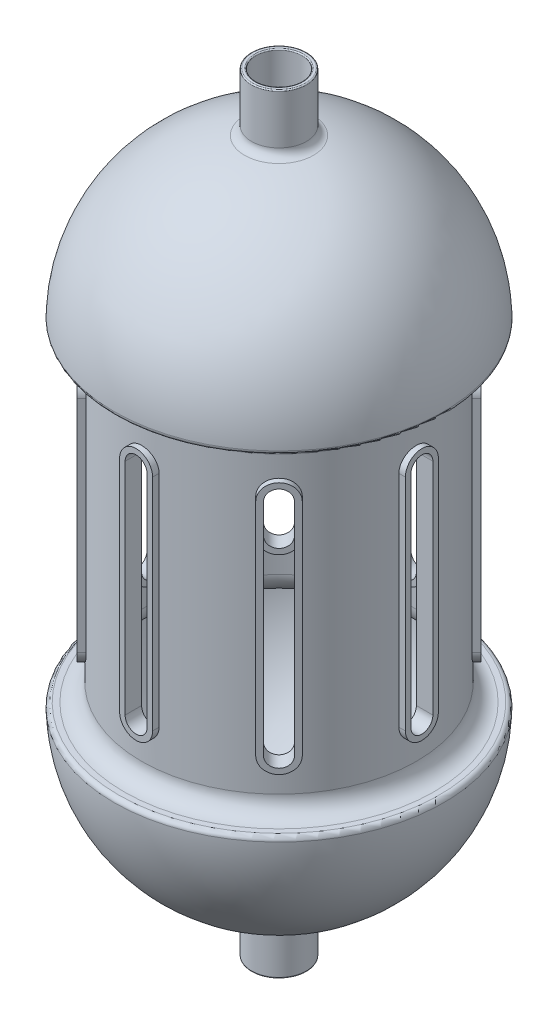
SolidWorks part; units mm, degrees
material "Thornel VCB-20 Carbon Cloth"
ref_plane "Front Plane" through (0, 0, 0) normal (0, 0, 1) x (1, 0, 0)
ref_plane "Top Plane" through (0, 0, 0) normal (0, 1, 0) x (1, 0, 0)
ref_plane "Right Plane" through (0, 0, 0) normal (1, 0, 0) x (0, 0, -1)
sketch "Sketch2" plane through (0, 0, 0) normal (0, 0, 1) x (1, 0, 0)
  line L0 (141, -155) -> (142.8286, -155)
  line L1 (141, -150) -> (145.9452, -150)
  line L2 (120, -134) -> (120, 134)
  line L3 (0, 349) -> (0, -349) construction
  line L4 (125, -134) -> (125, 134)
  line L5 (-125, -150) -> (125, 150) construction
  line L6 (-125, 150) -> (125, -150) construction
  line L7 (141, 150) -> (145.9452, 150)
  line L8 (141, 155) -> (142.8286, 155)
  line L9 (141, -155) -> (144.9138, -155) construction
  line L10 (141, 155) -> (144.9138, 155) construction
  line L11 (25, 304.5154) -> (25, 349)
  line L12 (22, 350) -> (24, 350)
  line L13 (22, -350) -> (24, -350)
  line L14 (21, 349) -> (21, 300.2265)
  line L15 (25, -304.5154) -> (25, -349)
  line L17 (21, -300.2265) -> (21, -349)
  arc A0 (31.3291, -296.6918) -> (149.9437, -154.1096) centre (0, -150) ccw
  arc A1 (149.9437, 154.1096) -> (31.3291, 296.6918) centre (0, 150) ccw
  arc A2 (149.9437, -154.1096) -> (145.9452, -150) centre (145.9452, -154) ccw
  arc A3 (149.9437, 154.1096) -> (145.9452, 150) centre (145.9452, 154) cw
  arc A4 (141, 150) -> (125, 134) centre (141, 134) ccw
  arc A5 (141, -150) -> (125, -134) centre (141, -134) cw
  arc A6 (27.4837, -292.3715) -> (144.8262, -157.0979) centre (0, -150) ccw
  arc A7 (144.9138, 155) -> (0, 295) centre (0, 150) ccw construction
  arc A8 (141, -155) -> (120, -134) centre (141, -134) cw
  arc A9 (141, 155) -> (120, 134) centre (141, 134) ccw
  arc A10 (21, 300.2265) -> (27.4837, 292.3715) centre (29, 300.2265) ccw
  arc A11 (144.8262, 157.0979) -> (27.4837, 292.3715) centre (0, 150) ccw
  arc A12 (0, -295) -> (144.9138, -155) centre (0, -150) ccw construction
  arc A13 (144.8262, -157.0979) -> (142.8286, -155) centre (142.8286, -157) ccw
  arc A14 (144.9138, -155) -> (144.9138, -155) centre (144.9138, -155) ccw construction
  arc A15 (144.8262, 157.0979) -> (142.8286, 155) centre (142.8286, 157) cw
  arc A16 (144.9138, 155) -> (144.9138, 155) centre (144.9138, 155) cw construction
  arc A17 (149.9437, 154.1096) -> (0, 300) centre (0, 150) ccw construction
  arc A18 (0, -300) -> (149.9437, -154.1096) centre (0, -150) ccw construction
  arc A19 (25, 304.5154) -> (31.3291, 296.6918) centre (33, 304.5154) ccw
  arc A20 (27.4837, -292.3715) -> (21, -300.2265) centre (29, -300.2265) ccw
  arc A21 (25, -304.5154) -> (31.3291, -296.6918) centre (33, -304.5154) cw
  arc A22 (25, -349) -> (24, -350) centre (24, -349) cw
  arc A23 (22, -350) -> (21, -349) centre (22, -349) cw
  arc A24 (25, 349) -> (24, 350) centre (24, 349) ccw
  arc A25 (22, 350) -> (21, 349) centre (22, 349) ccw
  point P0 (0, 0)
  dimension "D3" = 4
  dimension "D4" = 16
  dimension "D5" = 2
  dimension "D6" = 2
  dimension "D7" = 8
  dimension "D8" = 8
  dimension "D9" = 8
  dimension "D10" = 8
  dimension "D11" = 1
  dimension "D12" = 1
  dimension "D13" = 1
  dimension "D14" = 1
  dimension "D1" = 250
  dimension "D2" = 300
revolve "Revolve2" add sketch "Sketch2" angle 360 about L3
ref_plane "Plane4" through (-125, 0, 0) normal (-1, 0, 0) x (0, 0, 1)
sketch "Sketch4" plane through (-125, 0, 0) normal (-1, 0, 0) x (0, 0, 1)
  line L0 (0, -100) -> (0, 100) construction
  line L1 (-10, -100) -> (-10, 100) construction
  line L2 (10, -100) -> (10, 100) construction
  line L3 (-15, -100) -> (-15, 100)
  line L4 (15, -100) -> (15, 100)
  arc A0 (-10, -100) -> (10, -100) centre (0, -100) ccw construction
  arc A1 (10, 100) -> (-10, 100) centre (0, 100) ccw construction
  arc A2 (15, 100) -> (-15, 100) centre (0, 100) ccw
  arc A3 (-15, -100) -> (15, -100) centre (0, -100) ccw
  point P2 (0, 0)
  dimension "D1" = 200
  dimension "D2" = 20
extrude "Boss-Extrude1" add sketch "Sketch4" against normal blind 10 and the other way blind 5
sketch "Sketch5" plane through (-130, 0, 0) normal (-1, 0, 0) x (0, 0, 1)
  line L0 (0, -100) -> (0, 100) construction
  line L1 (-10, -100) -> (-10, 100)
  line L2 (10, -100) -> (10, 100)
  arc A0 (-10, -100) -> (10, -100) centre (0, -100) ccw
  arc A1 (10, 100) -> (-10, 100) centre (0, 100) ccw
  point P2 (0, 0)
  dimension "D1" = 200
  dimension "D2" = 20
extrude "Cut-Extrude4" cut sketch "Sketch5" against normal up to next (15 mm away)
pattern_circular "CirPattern1" count 8 over 360 about axis through (0, 0, 0) along (0, 1, 0) of "Boss-Extrude1", "Cut-Extrude4"
